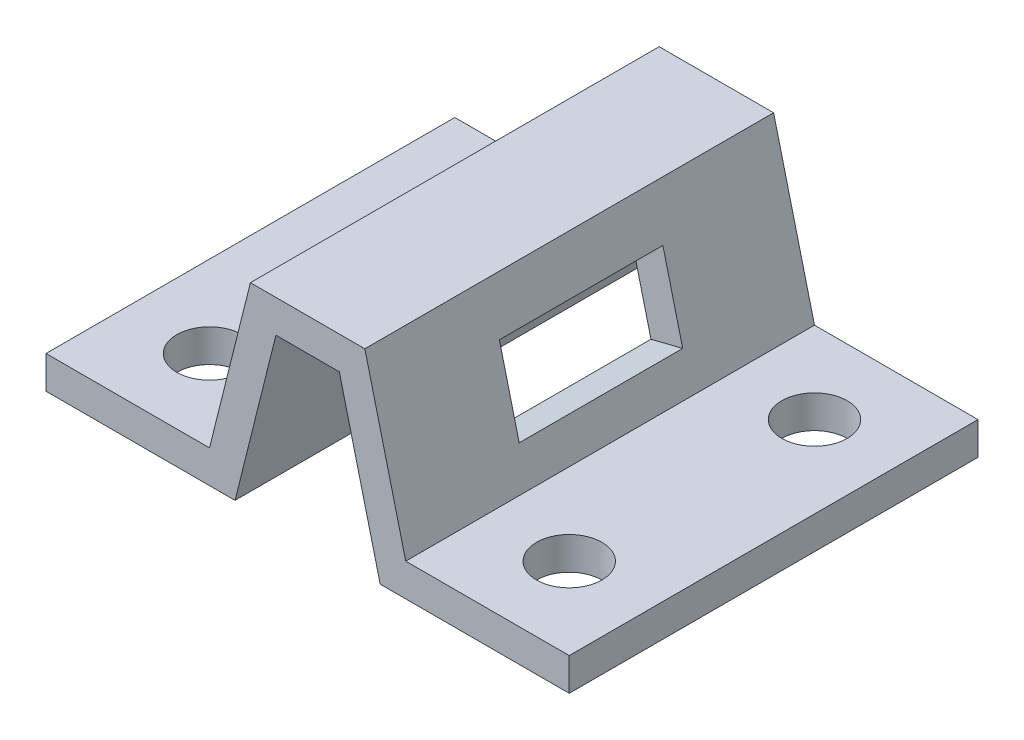
SolidWorks part; units mm, degrees
ref_plane "Front Plane" through (0, 0, 0) normal (0, 0, 1) x (1, 0, 0)
ref_plane "Top Plane" through (0, 0, 0) normal (0, 1, 0) x (1, 0, 0)
ref_plane "Right Plane" through (0, 0, 0) normal (1, 0, 0) x (0, 0, -1)
sketch "Sketch2" plane through (0, 0, 0) normal (0, 0, 1) x (1, 0, 0)
  line L0 (0, 75.7058) -> (0, -79.8931) construction
  line L1 (-141.2253, 0) -> (135.101, 0) construction
  line L2 (-17.5, 60) -> (17.5, 60)
  line L3 (80, 10) -> (80, 0)
  line L4 (75, 0) -> (75, 0) construction
  line L5 (80, 10) -> (30, 10)
  line L6 (30, 10) -> (17.5, 60)
  line L7 (80, 0) -> (22.1922, 0)
  line L8 (22.1922, 0) -> (9.6922, 50)
  line L9 (9.6922, 50) -> (0, 50)
  line L10 (75, 10) -> (80, 10) construction
  line L11 (75, 0) -> (22.1922, 0) construction
  line L12 (-80, 10) -> (-80, 0)
  line L13 (-80, 0) -> (-22.1922, 0)
  line L14 (-80, 10) -> (-30, 10)
  line L15 (-30, 10) -> (-17.5, 60)
  line L16 (-22.1922, 0) -> (-9.6922, 50)
  line L17 (-9.6922, 50) -> (0, 50)
  line L19 (17.5, 60) -> (0, 60) construction
  point P8 (0, 60)
  point P10 (80, 5)
  dimension "D1" = 160
  dimension "D2" = 35
  dimension "D3" = 10
  dimension "D4" = 10
  dimension "D5" = 50
extrude "Boss-Extrude1" add sketch "Sketch2" along normal mid plane 125
sketch "Sketch3" plane through (0, 10, 0) normal (0, 1, 0) x (1, 0, 0)
  line L0 (80, 62.5) -> (30, 62.5) construction
  line L1 (80, -62.5) -> (80, 62.5) construction
  line L2 (0, 85.228) -> (0, -94.0081) construction
  circle A0 centre (55, 37.5) radius 10
  circle A1 centre (-55, 37.5) radius 10
  circle A2 centre (-55, -37.5) radius 10
  circle A3 centre (55, -37.5) radius 10
  dimension "D1" = 20
  dimension "D2" = 25
  dimension "D3" = 25
  dimension "D4" = 2
  dimension "D5" = 2
extrude "Cut-Extrude1" cut sketch "Sketch3" against normal blind 125
sketch "Sketch4" plane through (30.5882, 7.6471, 0) normal (0.9701, 0.2425, 0) x (0, 0, -1)
  line L0 (62.5, 2.4254) -> (62.5, 53.9642) construction
  line L1 (-25, 38.9642) -> (25, 38.9642)
  line L2 (-25, 38.9642) -> (-25, 13.9642)
  line L3 (-25, 13.9642) -> (25, 13.9642)
  line L4 (25, 38.9642) -> (25, 13.9642)
  line L5 (-25, 38.9642) -> (25, 13.9642) construction
  line L6 (-25, 13.9642) -> (25, 38.9642) construction
  line L8 (-62.5, 53.9642) -> (62.5, 53.9642) construction
  point P0 (0, 26.4642)
  dimension "D1" = 50
  dimension "D2" = 37.5
  dimension "D3" = 15
  dimension "D4" = 25
extrude "Cut-Extrude2" cut sketch "Sketch4" against normal blind 10
sketch "Sketch5" plane through (-30.5882, 7.6471, 0) normal (-0.9701, 0.2425, 0) x (0, 0, 1)
  line L0 (62.5, 53.9642) -> (-62.5, 53.9642) construction
  line L1 (-25, 38.9642) -> (25, 38.9642)
  line L2 (-25, 38.9642) -> (-25, 13.9642)
  line L3 (-25, 13.9642) -> (25, 13.9642)
  line L4 (25, 38.9642) -> (25, 13.9642)
  line L5 (-25, 38.9642) -> (25, 13.9642) construction
  line L6 (-25, 13.9642) -> (25, 38.9642) construction
  point P0 (0, 26.4642)
  dimension "D1" = 15
  dimension "D2" = 25
  dimension "D3" = 37.5
  dimension "D4" = 50
extrude "Cut-Extrude3" cut sketch "Sketch5" against normal blind 10
